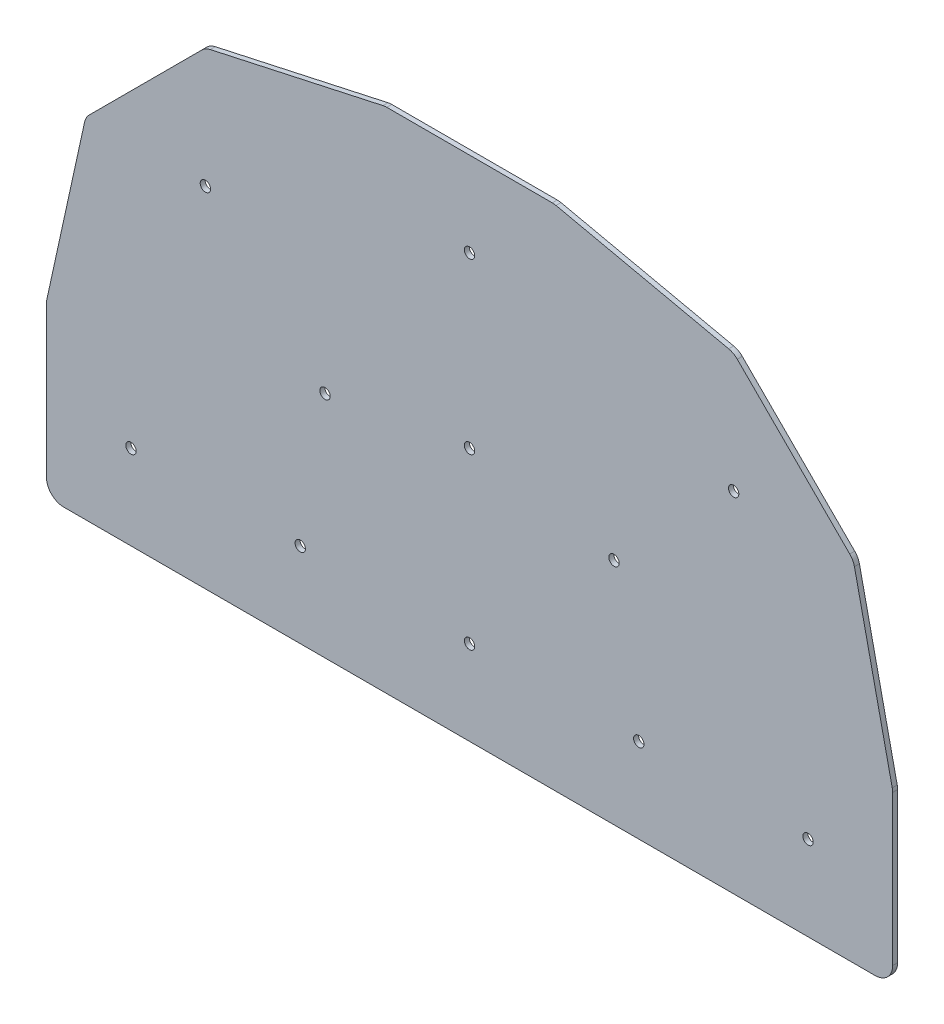
SolidWorks part; units mm, degrees
ref_plane "Front Plane" through (0, 0, 0) normal (0, 0, 1) x (1, 0, 0)
ref_plane "Top Plane" through (0, 0, 0) normal (0, 1, 0) x (1, 0, 0)
ref_plane "Right Plane" through (0, 0, 0) normal (1, 0, 0) x (0, 0, -1)
ref_plane "Plane1" through (0, 0, 0) normal (0, 0, -1) x (-1, 0, 0)
sketch "Sketch1" plane through (0, 0, 0) normal (0, 0, -1) x (-1, 0, 0)
  line L0 (-129.3812, 0) -> (129.3812, 0)
  line L1 (134.9375, 5.5562) -> (134.9375, 53.3738)
  line L2 (134.8089, 54.5622) -> (122.7508, 109.6344)
  line L3 (121.252, 112.3749) -> (85.3874, 148.2395)
  line L4 (82.6469, 149.7383) -> (27.5747, 161.7964)
  line L5 (26.3863, 161.925) -> (-26.3863, 161.925)
  line L6 (-27.5747, 161.7964) -> (-82.6469, 149.7383)
  line L7 (-85.3874, 148.2395) -> (-121.252, 112.3749)
  line L8 (-122.7508, 109.6344) -> (-134.8089, 54.5622)
  line L9 (-134.9375, 53.3738) -> (-134.9375, 5.5563)
  circle A0 centre (-53.975, 26.9875) radius 1.651
  circle A1 centre (53.975, 26.9875) radius 1.651
  circle A2 centre (46.0705, 73.058) radius 1.651
  circle A3 centre (84.2366, 111.2241) radius 1.651
  circle A4 centre (-46.0705, 73.058) radius 1.651
  circle A5 centre (-84.2366, 111.2241) radius 1.651
  circle A6 centre (-107.95, 26.9875) radius 1.651
  circle A7 centre (107.95, 26.9875) radius 1.651
  circle A8 centre (0, 80.9625) radius 1.651
  circle A9 centre (0, 134.9375) radius 1.651
  circle A10 centre (0, 26.9875) radius 1.651
  arc A11 (-134.9375, 5.5563) -> (-129.3812, 0) centre (-129.3812, 5.5563) ccw
  arc A12 (129.3812, 0) -> (134.9375, 5.5562) centre (129.3812, 5.5563) ccw
  arc A13 (134.9375, 53.3738) -> (134.8089, 54.5622) centre (129.3812, 53.3738) ccw
  arc A14 (122.7508, 109.6344) -> (121.252, 112.3749) centre (117.3231, 108.446) ccw
  arc A15 (85.3874, 148.2395) -> (82.6469, 149.7383) centre (81.4585, 144.3106) ccw
  arc A16 (27.5747, 161.7964) -> (26.3863, 161.925) centre (26.3863, 156.3687) ccw
  arc A17 (-26.3863, 161.925) -> (-27.5747, 161.7964) centre (-26.3863, 156.3687) ccw
  arc A18 (-82.6469, 149.7383) -> (-85.3874, 148.2395) centre (-81.4585, 144.3106) ccw
  arc A19 (-121.252, 112.3749) -> (-122.7508, 109.6344) centre (-117.3231, 108.446) ccw
  arc A20 (-134.8089, 54.5622) -> (-134.9375, 53.3738) centre (-129.3812, 53.3738) ccw
extrude "Boss-Extrude1" add sketch "Sketch1" against normal blind 1.5875
